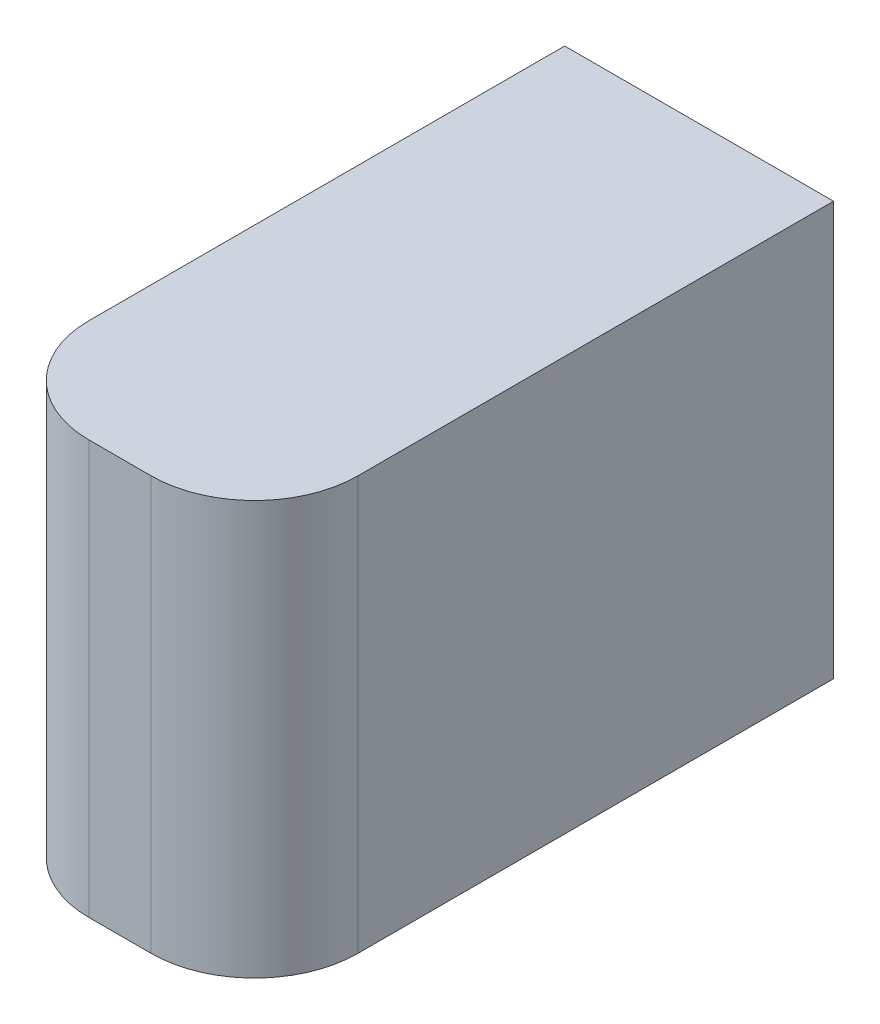
SolidWorks part; units mm, degrees
ref_plane "Front Plane" through (0, 0, 0) normal (0, 0, 1) x (1, 0, 0)
ref_plane "Top Plane" through (0, 0, 0) normal (0, 1, 0) x (1, 0, 0)
ref_plane "Right Plane" through (0, 0, 0) normal (1, 0, 0) x (0, 0, -1)
sketch "Sketch1" plane through (0, 0, 0) normal (0, 0, 1) x (1, 0, 0)
  line L1 (-1.3, 2) -> (1.3, 2)
  line L2 (-1.3, 2) -> (-1.3, -2)
  line L3 (-1.3, -2) -> (1.3, -2)
  line L4 (1.3, 2) -> (1.3, -2)
  point P4 (0, 2)
  point P6 (1.3, 0)
  dimension "D1" = 4
  dimension "D2" = 2.6
extrude "Extrude1" add sketch "Sketch1" along normal blind 5.6
fillet "Fillet2" radius 1 2 edges at (1.3, 0, 5.6) (-1.3, 0, 5.6)
